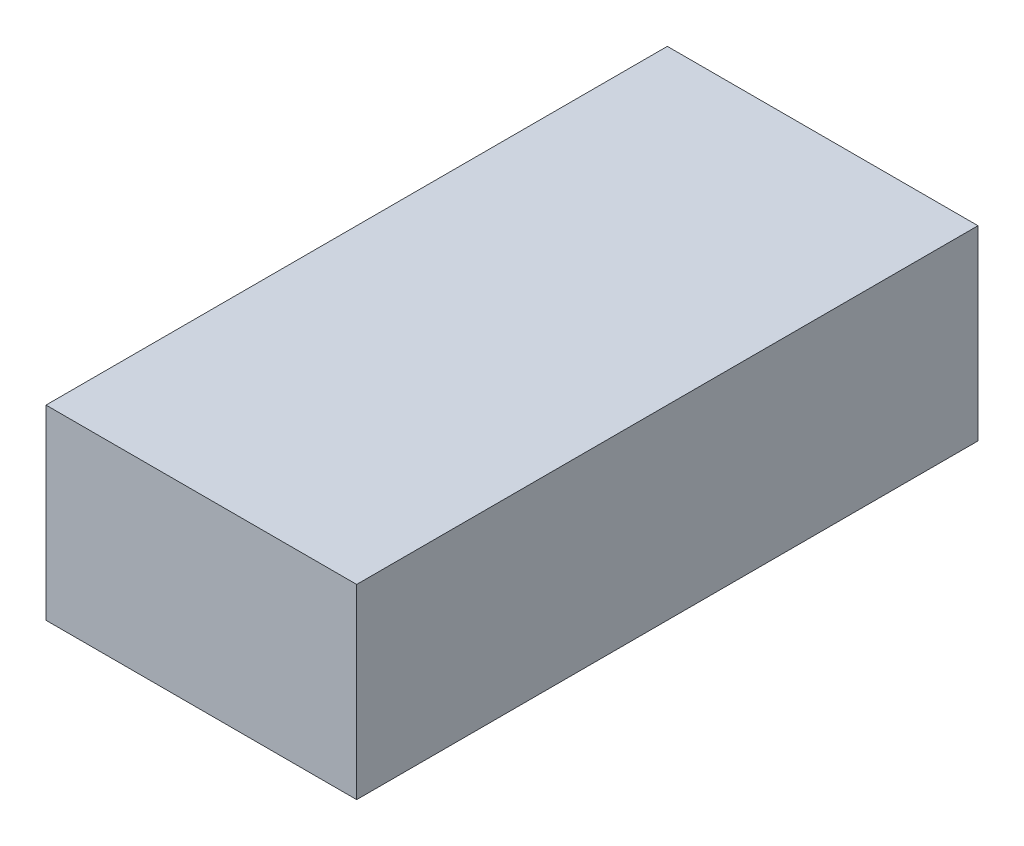
SolidWorks part; units mm, degrees
ref_plane "Front Plane" through (0, 0, 0) normal (0, 0, 1) x (1, 0, 0)
ref_plane "Top Plane" through (0, 0, 0) normal (0, 1, 0) x (1, 0, 0)
ref_plane "Right Plane" through (0, 0, 0) normal (1, 0, 0) x (0, 0, -1)
sketch "Sketch2" plane through (0, 0, 0) normal (1, 0, 0) x (0, 0, -1)
  line L3 (-262.7936, 0) -> (0, 0)
  line L4 (0, 0) -> (203.2, 0)
  line L6 (203.2, 0) -> (203.2, 81.9)
  line L7 (203.2, 81.9) -> (188.2, 81.9)
  line L8 (188.2, 81.9) -> (188.2, 20)
  line L9 (188.2, 20) -> (0, 20)
  line L10 (0, 20) -> (0, 133.7)
  line L11 (0, 133.7) -> (-115, 133.7)
  line L12 (-115, 133.7) -> (-171.1938, 94.3527)
  line L13 (-171.1938, 94.3527) -> (-262.7936, 81.4791)
  line L18 (-262.7936, 81.4791) -> (-262.7936, 31.4791)
  line L19 (-262.7936, 31.4791) -> (-262.7936, 0) construction
  arc A2 (-262.7936, 31.4791) -> (-262.7936, 0) centre (-255.1441, 15.7396) ccw
  dimension "D12" = 17.5
  dimension "D2" = 113.7
  dimension "D3" = 20
  dimension "D4" = 35
  dimension "D5" = 153
  dimension "D6" = 203.2
  dimension "D7" = 15
  dimension "D8" = 61.9
  dimension "D9" = 92.5
  dimension "D10" = 68.6
  dimension "D11" = 50
  dimension "D13" = 115
extrude "Boss-Extrude1" add sketch "Sketch2" along normal mid plane 138
sketch "Sketch4" plane through (0, 20, 0) normal (0, 1, 0) x (1, 0, 0)
  line L0 (69, 188.2) -> (-69, 188.2) construction
  line L1 (69, 0) -> (54, 0)
  line L2 (69, 0) -> (69, 188.2)
  line L3 (69, 188.2) -> (54, 188.2)
  line L4 (54, 0) -> (54, 188.2)
  dimension "D1" = 15
extrude "Boss-Extrude2" add sketch "Sketch4" along normal up to surface (61.9 mm away) up to face at (0, 81.9, -195.7)
mirror "Mirror1" about plane through (0, 0, 0) normal (1, 0, 0) of "Boss-Extrude2"
sketch "Sketch5" plane through (69, 0, 0) normal (1, 0, 0) x (0, 0, -1)
  line L0 (-262.7936, 0) -> (203.2, 0) construction
  line L1 (-224.9441, 0) -> (-160.3441, 0)
  line L2 (28.0559, 0) -> (92.6559, 0)
  arc A0 (-224.9441, 0) -> (-160.3441, 0) centre (-192.6441, 0) ccw
  arc A1 (28.0559, 0) -> (92.6559, 0) centre (60.3559, 0) ccw
  arc A2 (-262.7936, 31.4791) -> (-262.7936, 0) centre (-255.1441, 15.7396) ccw construction
  point P11 (-272.6441, 15.7396)
  dimension "D3" = 32.3
  dimension "D1" = 333
  dimension "D2" = 80
extrude "Boss-Extrude3" add sketch "Sketch5" against normal blind 20.4
mirror "Mirror2" about plane through (0, 0, 0) normal (1, 0, 0) of "Boss-Extrude3"
fillet "Fillet1" radius 10 5 edges at (0, 133.7, 0) (0, 133.7, 115) (0, 94.3527, 171.1938) (0, 81.4791, 262.7936) (0, 31.4791, 262.7936)
sketch "Sketch6" plane through (0, 0, 0) normal (1, 0, 0) x (0, 0, -1)
  line L1 (-2272.5135, -32.3) -> (7727.4865, -32.3)
  line L2 (-2272.5135, -32.3) -> (-2272.5135, 2967.7)
  line L3 (-2272.5135, 2967.7) -> (7727.4865, 2967.7)
  line L4 (7727.4865, -32.3) -> (7727.4865, 2967.7)
  arc A0 (-266.3756, 29.1598) -> (-262.7936, 0) centre (-255.1441, 15.7396) ccw construction
  arc A1 (-224.9441, 0) -> (-160.3441, 0) centre (-192.6441, 0) ccw construction
  point P7 (-272.5135, 13.6059)
  point P11 (-192.6441, -32.3)
  dimension "D1" = 3000
  dimension "D2" = 10000
  dimension "D3" = 2000
extrude "Boss-Extrude4" add sketch "Sketch6" along normal mid plane 5000 separate body
sketch "Sketch7" plane through (0, 0, 0) normal (1, 0, 0) x (0, 0, -1)
  line L0 (-192.6441, 0) -> (-192.6441, -32.3) construction
  line L1 (-430.6441, -32.3) -> (521.3559, -32.3)
  line L2 (-430.6441, -32.3) -> (-430.6441, 443.7)
  line L3 (-430.6441, 443.7) -> (521.3559, 443.7)
  line L4 (521.3559, -32.3) -> (521.3559, 443.7)
  arc A0 (-224.9441, 0) -> (-160.3441, 0) centre (-192.6441, 0) ccw construction
  dimension "D1" = 476
  dimension "D2" = 952
  dimension "D3" = 238
extrude "Boss-Extrude5" add sketch "Sketch7" along normal mid plane 476 separate body
